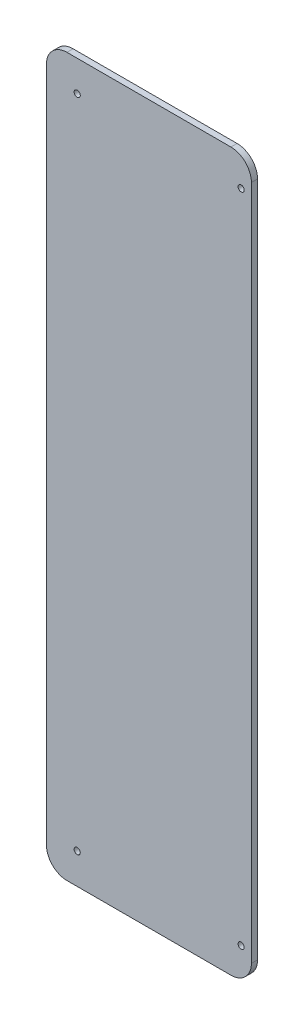
SolidWorks part; units mm, degrees
ref_plane "Plan de face" through (0, 0, 0) normal (0, 0, 1) x (1, 0, 0)
ref_plane "Plan de dessus" through (0, 0, 0) normal (0, 1, 0) x (1, 0, 0)
ref_plane "Plan de droite" through (0, 0, 0) normal (1, 0, 0) x (0, 0, -1)
sketch "Esquisse1" plane through (0, 0, 0) normal (0, 0, 1) x (1, 0, 0)
  line L1 (10, 0) -> (90, 0)
  line L2 (0, 10) -> (0, 340)
  line L3 (10, 350) -> (90, 350)
  line L4 (100, 10) -> (100, 340)
  circle A0 centre (95, 335) radius 1.5
  circle A1 centre (15, 335) radius 1.5
  circle A2 centre (95, 15) radius 1.5
  circle A3 centre (15, 15) radius 1.5
  arc A4 (10, 0) -> (0, 10) centre (10, 10) cw
  arc A5 (90, 0) -> (100, 10) centre (90, 10) ccw
  arc A6 (90, 350) -> (100, 340) centre (90, 340) cw
  arc A7 (0, 340) -> (10, 350) centre (10, 340) cw
  point P15 (0, 0)
  point P18 (100, 0)
  point P23 (0, 350)
  dimension "D3" = 3
  dimension "D4" = 3
  dimension "D5" = 3
  dimension "D6" = 3
  dimension "D15" = 10
  dimension "D1" = 350
  dimension "D2" = 100
  dimension "D7" = 15
  dimension "D8" = 15
  dimension "D9" = 15
  dimension "D10" = 95
  dimension "D11" = 15
  dimension "D12" = 15
  dimension "D13" = 15
  dimension "D14" = 95
extrude "Boss.-Extru.1" add sketch "Esquisse1" along normal blind 3
